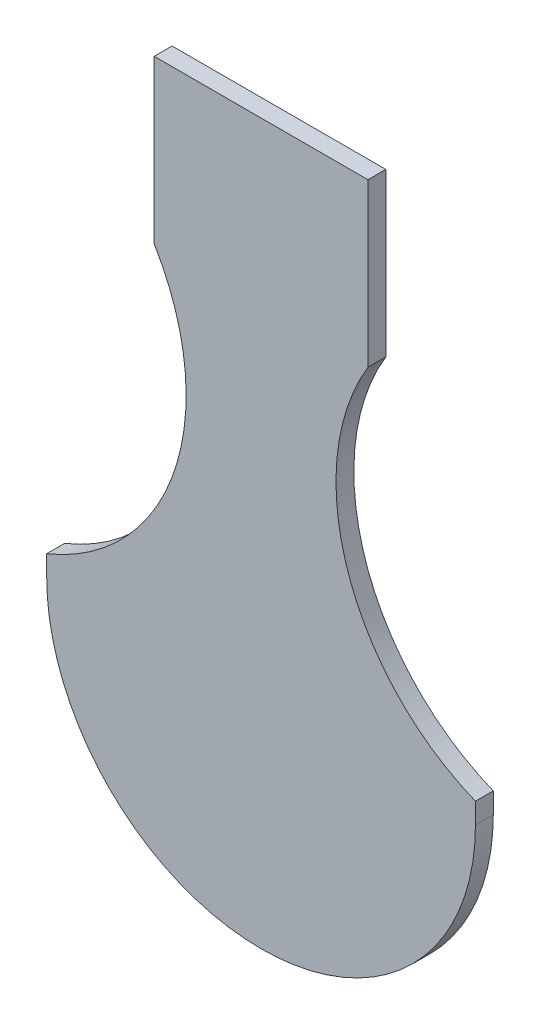
SolidWorks part; units mm, degrees
ref_plane "Front Plane" through (0, 0, 0) normal (0, 0, 1) x (1, 0, 0)
ref_plane "Top Plane" through (0, 0, 0) normal (0, 1, 0) x (1, 0, 0)
ref_plane "Right Plane" through (0, 0, 0) normal (1, 0, 0) x (0, 0, -1)
sketch "Sketch1" plane through (0, 0, 0) normal (0, 0, 1) x (1, 0, 0)
  line L9 (60, 65.7771) -> (60, 0)
  line L10 (60, 0) -> (-60, 0)
  line L11 (0, 0) -> (0, 180.4532) construction
  line L12 (-60, 65.7771) -> (-60, 0)
  line L14 (-29.9097, 155.9063) -> (-29.9096, 201.3963)
  line L15 (29.9097, 155.9063) -> (29.9097, 201.3963)
  line L16 (-29.9096, 201.3963) -> (29.9097, 201.3963)
  line L17 (83.4736, 123.7015) -> (0, 95.8332) construction
  arc A0 (60, 65.7771) -> (29.9097, 155.9063) centre (83.4736, 123.7015) cw
  arc A2 (-60, 65.7771) -> (-29.9097, 155.9063) centre (-83.4736, 123.7015) ccw
  circle A3 centre (0, 95.8332) radius 60 construction
  circle A4 centre (0, 180.4532) radius 24.62 construction
  point P13 (0, 0)
  point P14 (0, 0)
  point P15 (0, 0)
  point P16 (0, 0)
  point P17 (0, 0)
  dimension "D1" = 120
  dimension "D2" = 62.5
  dimension "D6" = 120
  dimension "D7" = 49.24
  dimension "D3" = 29.9097
  dimension "D4" = 83.4736
  dimension "D5" = 59.8193
  dimension "D8" = 45.49
  dimension "D9" = 45.49
  dimension "D10" = 65.7771
extrude "Boss-Extrude1" add sketch "Sketch1" along normal blind 5
sketch "Sketch2" plane through (0, 0, 5) normal (0, 0, 1) x (1, 0, 0)
  line L0 (-60, 0) -> (60, 0) construction
  line L1 (60, 0) -> (60, 65.7771) construction
  line L2 (-60, 60) -> (-60, -14.1553)
  line L3 (-60, -14.1553) -> (60, -14.1553)
  line L4 (60, -14.1553) -> (60, 60)
  circle A0 centre (0, 60) radius 60 construction
  arc A1 (60, 60) -> (-60, 60) centre (0, 60) cw
  dimension "D1" = 120
extrude "Cut-Extrude1" cut sketch "Sketch2" against normal through all
